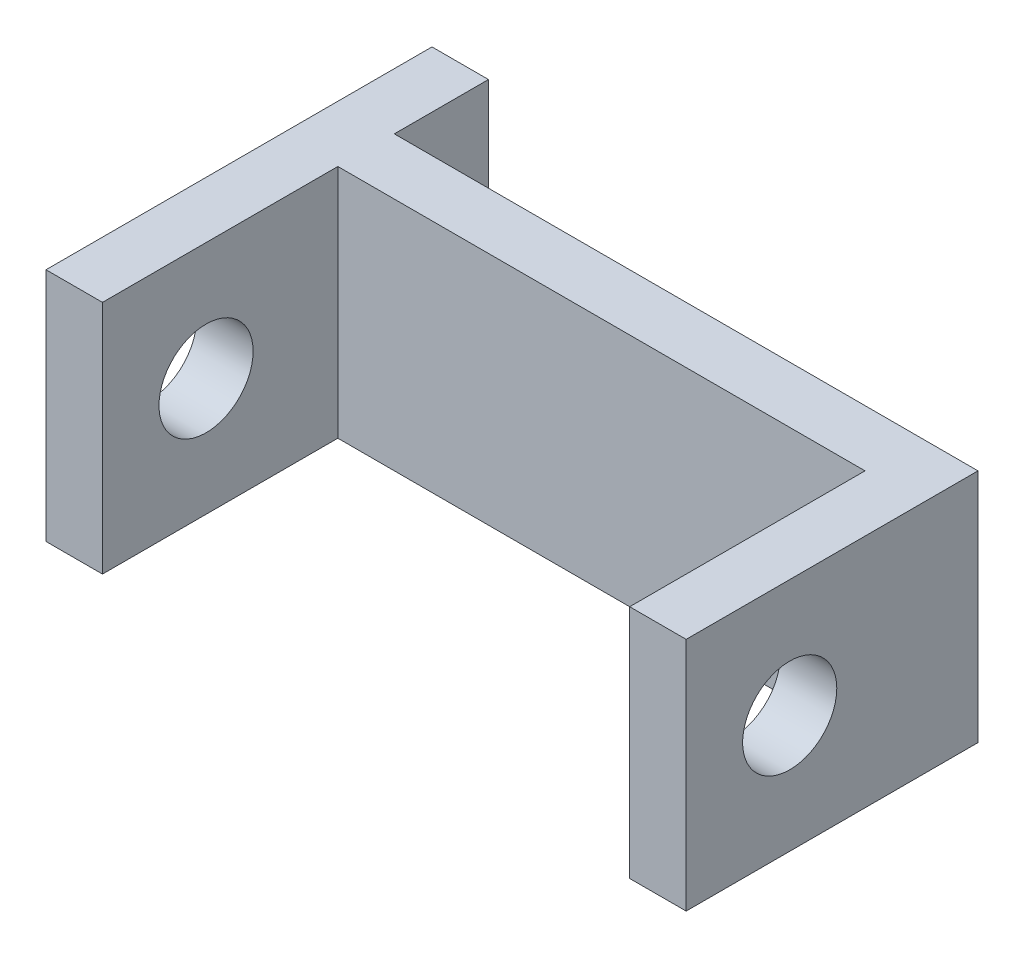
SolidWorks part; units mm, degrees
ref_plane "Front" through (0, 0, 0) normal (0, 0, 1) x (1, 0, 0)
ref_plane "Top" through (0, 0, 0) normal (0, 1, 0) x (1, 0, 0)
ref_plane "Right" through (0, 0, 0) normal (1, 0, 0) x (0, 0, -1)
sketch "草图1" plane through (0, 0, 0) normal (0, 0, 1) x (1, 0, 0)
  line L0 (15.088, 5) -> (1.488, 5)
  line L6 (15.088, 0) -> (15.088, 5)
  line L7 (1.488, 5) -> (1.488, 0)
  line L8 (1.488, 0) -> (15.088, 0)
extrude "凸台-拉伸1" add sketch "草图1" along normal blind 1.2
sketch "草图2" plane through (0, 0, 1.2) normal (0, 0, -1) x (-1, 0, 0)
  line L6 (-15.088, 5) -> (-1.488, 5) construction
  line L7 (-15.088, 0) -> (-13.888, 0)
  line L8 (-15.088, 0) -> (-15.088, 5)
  line L9 (-15.088, 5) -> (-13.888, 5)
  line L10 (-13.888, 0) -> (-13.888, 5)
  line L11 (-1.488, 0) -> (-15.088, 0) construction
  line L12 (-1.488, 5) -> (-2.688, 5)
  line L13 (-1.488, 5) -> (-1.488, 0)
  line L14 (-1.488, 0) -> (-2.688, 0)
  line L15 (-2.688, 5) -> (-2.688, 0)
extrude "凸台-拉伸2" add sketch "草图2" against normal blind 5
sketch "草图3" plane through (15.088, 0, 0) normal (1, 0, 0) x (0, 0, -1)
  line L1 (0, 0) -> (0, 5) construction
  circle A0 centre (-4, 2.5) radius 1
  dimension "D1" = 4
extrude "切除-拉伸1" cut sketch "草图3" against normal blind 14
sketch "草图5" plane through (0, 0, 0) normal (0, 0, -1) x (-1, 0, 0)
  line L0 (-15.088, 5) -> (-1.488, 5) construction
  line L1 (-1.488, 0) -> (-2.688, 0)
  line L2 (-1.488, 0) -> (-1.488, 5)
  line L3 (-1.488, 5) -> (-2.688, 5)
  line L4 (-2.688, 0) -> (-2.688, 5)
extrude "凸台-拉伸3" add sketch "草图5" along normal blind 2
